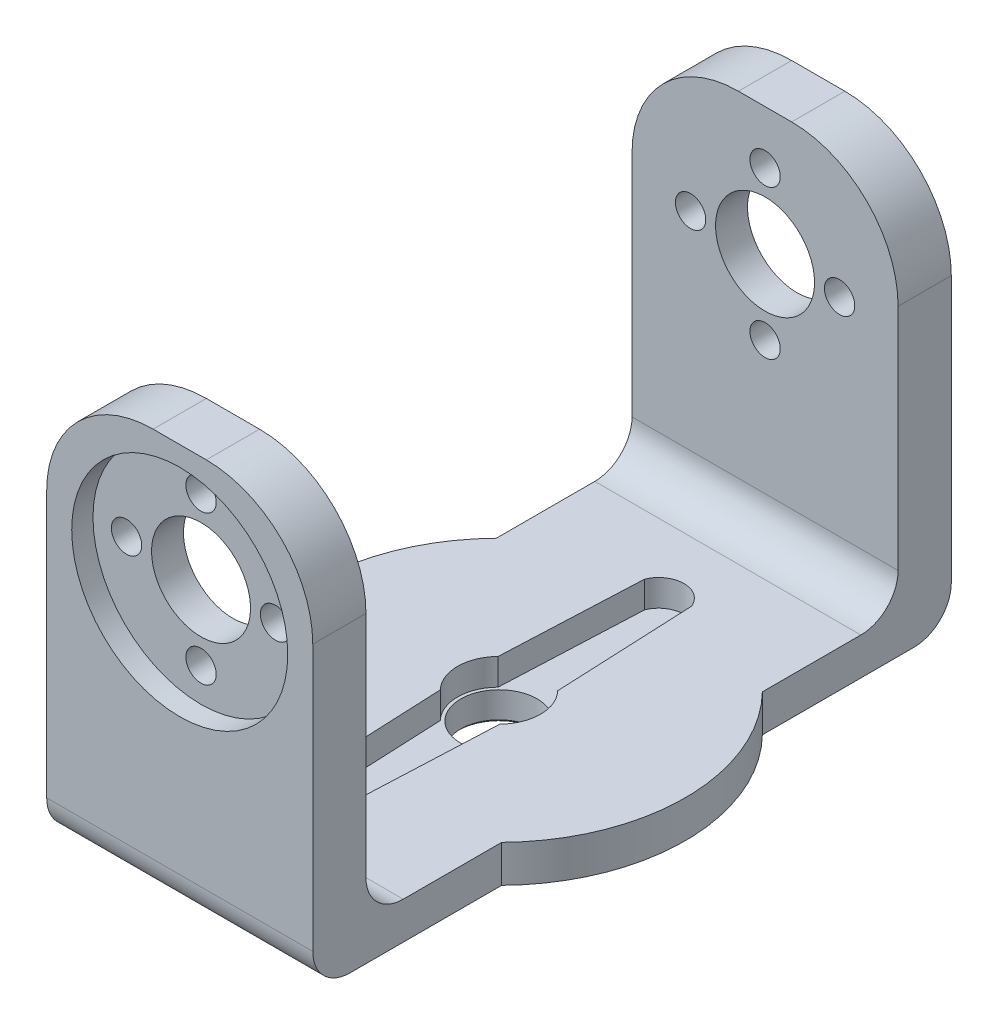
SolidWorks part; units mm, degrees
ref_plane "Alzado" through (0, 0, 0) normal (0, 0, 1) x (1, 0, 0)
ref_plane "Planta" through (0, 0, 0) normal (0, 1, 0) x (1, 0, 0)
ref_plane "Vista lateral" through (0, 0, 0) normal (1, 0, 0) x (0, 0, -1)
ref_plane "Plano1" through (0, 0, 30) normal (0, 0, 1) x (1, 0, 0)
sketch "Croquis1" plane through (0, 0, 0) normal (0, 1, 0) x (1, 0, 0)
  line L0 (1.9972, 12.1065) -> (2.53, 2.1187) construction
  line L1 (-1.9972, 12.1065) -> (-2.53, 2.1187) construction
  line L2 (-1.9972, -12.1065) -> (-2.53, -2.1187) construction
  line L3 (1.9972, -12.1065) -> (2.53, -2.1187) construction
  line L4 (1.9972, 12.1065) -> (2.53, 2.1187)
  line L5 (-1.9972, 12.1065) -> (-2.53, 2.1187)
  line L6 (-1.9972, -12.1065) -> (-2.53, -2.1187)
  line L7 (1.9972, -12.1065) -> (2.53, -2.1187)
  circle A0 centre (0, 0) radius 17.5
  circle A1 centre (0, 0) radius 1.65
  arc A2 (2.53, -2.1187) -> (2.53, 2.1187) centre (0, 0) ccw construction
  arc A3 (1.9972, 12.1065) -> (-1.9972, 12.1065) centre (0, 12) ccw construction
  arc A4 (-2.53, 2.1187) -> (-2.53, -2.1187) centre (0, 0) ccw construction
  arc A5 (-1.9972, -12.1065) -> (1.9972, -12.1065) centre (0, -12) ccw construction
  arc A6 (2.53, -2.1187) -> (2.53, 2.1187) centre (0, 0) ccw
  arc A7 (1.9972, 12.1065) -> (-1.9972, 12.1065) centre (0, 12) ccw
  arc A8 (-2.53, 2.1187) -> (-2.53, -2.1187) centre (0, 0) ccw
  arc A9 (-1.9972, -12.1065) -> (1.9972, -12.1065) centre (0, -12) ccw
  dimension "D1" = 35
  dimension "D2" = 3.3
extrude "Saliente-Extruir1" add sketch "Croquis1" along normal blind 3.5 contours A0 A1 | L6 A9 L7 A6 L4 A7 L5 A8 A1
sketch "Croquis2" plane through (0, 3.5, 0) normal (0, 1, 0) x (1, 0, 0)
  line L0 (-1.9972, -12.1065) -> (-2.53, -2.1187) construction
  line L1 (1.9972, -12.1065) -> (2.53, -2.1187) construction
  line L2 (1.9972, 12.1065) -> (2.53, 2.1187) construction
  line L3 (-1.9972, 12.1065) -> (-2.53, 2.1187) construction
  line L4 (-1.9972, -12.1065) -> (-2.53, -2.1187)
  line L5 (1.9972, -12.1065) -> (2.53, -2.1187)
  line L6 (1.9972, 12.1065) -> (2.53, 2.1187)
  line L7 (-1.9972, 12.1065) -> (-2.53, 2.1187)
  arc A1 (-2.53, 2.1187) -> (-2.53, -2.1187) centre (0, 0) ccw construction
  arc A2 (-1.9972, -12.1065) -> (1.9972, -12.1065) centre (0, -12) ccw construction
  arc A3 (2.53, -2.1187) -> (2.53, 2.1187) centre (0, 0) ccw construction
  arc A4 (1.9972, 12.1065) -> (-1.9972, 12.1065) centre (0, 12) ccw construction
  arc A5 (-2.53, 2.1187) -> (-2.53, -2.1187) centre (0, 0) ccw
  arc A6 (-1.9972, -12.1065) -> (1.9972, -12.1065) centre (0, -12) ccw
  arc A7 (2.53, -2.1187) -> (2.53, 2.1187) centre (0, 0) ccw
  arc A8 (1.9972, 12.1065) -> (-1.9972, 12.1065) centre (0, 12) ccw
extrude "Cortar-Extruir1" cut sketch "Croquis2" against normal blind 2.5
sketch "Croquis4" plane through (0, 1, 0) normal (0, 1, 0) x (1, 0, 0)
  circle A1 centre (0, 0) radius 3.3 construction
  circle A2 centre (0, 0) radius 3.3 construction
  circle A3 centre (0, 0) radius 3.6
  dimension "D1" = 0.3
extrude "Cortar-Extruir2" cut sketch "Croquis4" against normal through all both and the other way through all
sketch "Croquis8" plane through (0, 3.5, 0) normal (0, 1, 0) x (1, 0, 0)
  line L0 (3.9, 0) -> (3.9493, 0) construction
  line L1 (1.9972, -12.1065) -> (2.5051, -2.5854) construction
  line L2 (-2.5051, -2.5854) -> (-1.9972, -12.1065) construction
  line L3 (1.9972, -12.1065) -> (2.5051, -2.5854) construction
  line L4 (-2.5051, -2.5854) -> (-1.9972, -12.1065) construction
  line L5 (-2.7955, -2.7194) -> (-2.3743, -12.1065)
  line L6 (2.3743, -12.1065) -> (2.7955, -2.7194)
  line L7 (-3.9, 0) -> (-3.9493, 0) construction
  line L8 (2.3743, -12.1065) -> (1.9972, -12.1065) construction
  line L9 (-1.9972, -12.1065) -> (-2.3743, -12.1065) construction
  line L10 (2.4826, -3.0078) -> (2.7826, -3.0078) construction
  line L11 (-2.4826, -3.0078) -> (-2.7826, -3.0078) construction
  line L12 (2.7955, -2.7194) -> (-2.7955, -2.7194) construction
  line L13 (2.3743, 12.1065) -> (2.7955, 2.7194)
  line L14 (-2.7955, 2.7194) -> (-2.3743, 12.1065)
  line L15 (0, 0) -> (-3.6, 0) construction
  line L16 (0, 0) -> (3.6, 0) construction
  line L17 (-3.6, 0) -> (-3.9, 0) construction
  line L18 (3.6, 0) -> (3.9, 0) construction
  arc A0 (-2.7955, 2.7194) -> (-2.7955, -2.7194) centre (0, 0) ccw
  arc A1 (-1.9972, -12.1065) -> (1.9972, -12.1065) centre (0, -12) ccw construction
  arc A2 (-1.9972, -12.1065) -> (1.9972, -12.1065) centre (0, -12) ccw construction
  arc A3 (-2.3743, -12.1065) -> (2.3743, -12.1065) centre (0, -12) ccw
  arc A4 (-2.7955, -2.7194) -> (-2.4826, -3.0078) centre (0, 0) ccw construction
  arc A5 (2.7955, -2.7194) -> (2.7955, 2.7194) centre (0, 0) ccw
  arc A6 (-2.4826, -3.0078) -> (2.4826, -3.0078) centre (0, 0) ccw construction
  arc A7 (2.4826, -3.0078) -> (2.7955, -2.7194) centre (0, 0) ccw construction
  arc A8 (-2.3743, 12.1065) -> (2.3743, 12.1065) centre (0, 12) cw
  arc A9 (2.5051, -2.5854) -> (2.5051, 2.5854) centre (0, 0) ccw construction
  arc A10 (2.5051, -2.5854) -> (2.5051, 2.5854) centre (0, 0) ccw construction
  arc A11 (-2.5051, 2.5854) -> (-2.5051, -2.5854) centre (0, 0) ccw construction
  arc A12 (-2.5051, 2.5854) -> (-2.5051, -2.5854) centre (0, 0) ccw construction
  dimension "D1" = 0.3
sketch "Croquis5" plane through (0, 0, 0) normal (0, -1, 0) x (1, 0, 0)
  circle A0 centre (0, 0) radius 5.6
  circle A1 centre (0, 0) radius 3.6 construction
  circle A2 centre (0, 0) radius 3.6
  dimension "D1" = 2
extrude "Saliente-Extruir2" add sketch "Croquis5" along normal offset from surface (1.7 mm away) 2.7 up to face at (0, 1, -8.073)
sketch "Croquis6" plane through (0, 0, 30) normal (0, 0, 1) x (1, 0, 0)
  line L0 (17.5, 3.5) -> (-17.5, 3.5) construction
  line L1 (-12.5, 3.5) -> (12.5, 3.5)
  line L2 (-12.5, 3.5) -> (-12.5, 0)
  line L3 (-12.5, 0) -> (12.5, 0)
  line L4 (12.5, 3.5) -> (12.5, 0)
  line L5 (-17.5, 0) -> (17.5, 0) construction
  line L6 (12.5, 0) -> (-12.5, 3.5) construction
  line L7 (-12.5, 0) -> (12.5, 3.5) construction
  line L8 (0, 3.5) -> (0, 1.75) construction
  dimension "D1" = 25
extrude "Saliente-Extruir3" add sketch "Croquis6" against normal up to surface (17.7526 mm away)
sketch "Croquis7" plane through (0, 3.5, 0) normal (0, 1, 0) x (1, 0, 0)
  line L0 (-19.25, -30) -> (19.25, -30) construction
  line L1 (12.5, -30) -> (-12.5, -30)
  line L2 (12.5, -30) -> (12.5, -25)
  line L3 (12.5, -25) -> (-12.5, -25)
  line L4 (-12.5, -30) -> (-12.5, -25)
  line L5 (-12.5, -12.2474) -> (-12.5, -30) construction
  line L6 (12.5, -12.2474) -> (12.5, -30) construction
  dimension "D1" = 5
extrude "Saliente-Extruir4" add sketch "Croquis7" along normal blind 35
fillet "Redondeo1" radius 3.5 2 edges at (0, 3.5, 25) (0, 0, 30)
mirror "Simetría1" about plane through (0, 0, 0) normal (0, 0, 1) of "Saliente-Extruir3", "Redondeo1", "Saliente-Extruir4"
ref_plane "Plano2" through (0, 0, 0) normal (0, 0, 1) x (1, 0, 0)
chamfer "Chaflán1" distance 0.254 angle 45 1 edges at (0, -1.7, 3.6)
extrude "Cortar-Extruir3" cut sketch "Croquis8" against normal up to surface (2.5 mm away) up to face at (0, 1, -8.073)
sketch "Croquis10" plane through (0, 0, 30) normal (0, 0, -1) x (-1, 0, 0)
  circle A0 centre (0, 26.5) radius 1
  circle A1 centre (0, 33.5) radius 1.425
  circle A2 centre (7, 26.5) radius 1.425
  circle A3 centre (-7, 26.5) radius 1.425
  circle A4 centre (0, 19.5) radius 1.425
  circle A5 centre (0, 26.5) radius 10.15
  dimension "D1" = 2.85
  dimension "D2" = 2
  dimension "D3" = 20.3
extrude "Cortar-Extruir7" cut sketch "Croquis10" along normal blind 2 contours A5 A3 A1 A0 A2 A4 | A2 | A0 | A1 | A3 | A4
sketch "Croquis11" plane through (0, 0, 25) normal (0, 0, -1) x (-1, 0, 0)
  line L0 (0, 0) -> (0, 38.5) construction
  line L1 (12.5, 38.5) -> (-12.5, 38.5) construction
  circle A0 centre (0, 26.5) radius 4.65
  dimension "D1" = 9.3
extrude "Cortar-Extruir8" cut sketch "Croquis11" against normal up to next
sketch "Croquis13" plane through (0, 0, 28) normal (0, 0, 1) x (1, 0, 0)
  circle A0 centre (0, 26.5) radius 10.15 construction
  circle A1 centre (0, 26.5) radius 10.15 construction
  circle A2 centre (0, 19.5) radius 1.425 construction
  circle A3 centre (7, 26.5) radius 1.425 construction
  circle A4 centre (0, 33.5) radius 1.425 construction
  circle A5 centre (-7, 26.5) radius 1.425 construction
  circle A6 centre (0, 19.5) radius 1.425
  circle A7 centre (7, 26.5) radius 1.425
  circle A8 centre (0, 33.5) radius 1.425
  circle A9 centre (-7, 26.5) radius 1.425
extrude "Cortar-Extruir9" cut sketch "Croquis13" against normal up to next
mirror "Simetría2" about plane through (0, 0, 0) normal (0, 0, 1) of "Cortar-Extruir9", "Cortar-Extruir8", "Cortar-Extruir7"
fillet "Redondeo2" radius 10 4 edges at (12.5, 38.5, 27.5) (-12.5, 38.5, 27.5) (12.5, 38.5, -27.5) (-12.5, 38.5, -27.5)
sketch "Croquis15" plane through (0, 3.5, 0) normal (0, 1, 0) x (1, 0, 0)
  line L0 (-2.3743, 12.1065) -> (-2.7955, 2.7194) construction
  line L1 (2.7955, 2.7194) -> (2.3743, 12.1065) construction
  line L2 (-2.3743, 12.1065) -> (-2.7955, 2.7194) construction
  line L3 (2.7955, 2.7194) -> (2.3743, 12.1065) construction
  line L4 (-3.9, 0) -> (3.9, 0) construction
  line L5 (0, 0) -> (0, 14.3766) construction
  line L6 (0, 14.3766) -> (0, 17.3766) construction
  line L7 (2.3743, 12.1065) -> (2.2046, 15.8879)
  line L8 (-2.3743, 12.1065) -> (-2.2046, 15.8879)
  line L9 (-2.3743, -12.1065) -> (-2.7955, -2.7194) construction
  line L10 (2.7955, -2.7194) -> (2.3743, -12.1065) construction
  line L11 (2.3743, -12.1065) -> (2.2046, -15.8879)
  line L12 (-2.3743, -12.1065) -> (-2.2046, -15.8879)
  arc A0 (2.7955, -2.7194) -> (2.7955, 2.7194) centre (0, 0) ccw construction
  arc A1 (-2.7955, 2.7194) -> (-2.7955, -2.7194) centre (0, 0) ccw construction
  arc A2 (2.7955, -2.7194) -> (2.7955, 2.7194) centre (0, 0) ccw construction
  arc A3 (-2.7955, 2.7194) -> (-2.7955, -2.7194) centre (0, 0) ccw construction
  arc A4 (2.3743, 12.1065) -> (-2.3743, 12.1065) centre (0, 12) ccw construction
  arc A5 (-2.2046, 15.8879) -> (2.2046, 15.8879) centre (0, 15) cw
  arc A6 (2.3743, 12.1065) -> (-2.3743, 12.1065) centre (0, 12) ccw construction
  arc A7 (-2.2046, -15.8879) -> (2.2046, -15.8879) centre (0, -15) ccw
  arc A8 (2.3743, 12.1065) -> (-2.3743, 12.1065) centre (0, 12) ccw
  arc A9 (-2.3743, -12.1065) -> (2.3743, -12.1065) centre (0, -12) ccw construction
  arc A10 (-2.3743, -12.1065) -> (2.3743, -12.1065) centre (0, -12) ccw
  point P29 (0, 0)
  dimension "D1" = 3
extrude "Cortar-Extruir10" cut sketch "Croquis15" against normal up to surface (2.5 mm away) up to face at (0, 1, 3.6)
equation "\"3.5.00mm\"=10"
